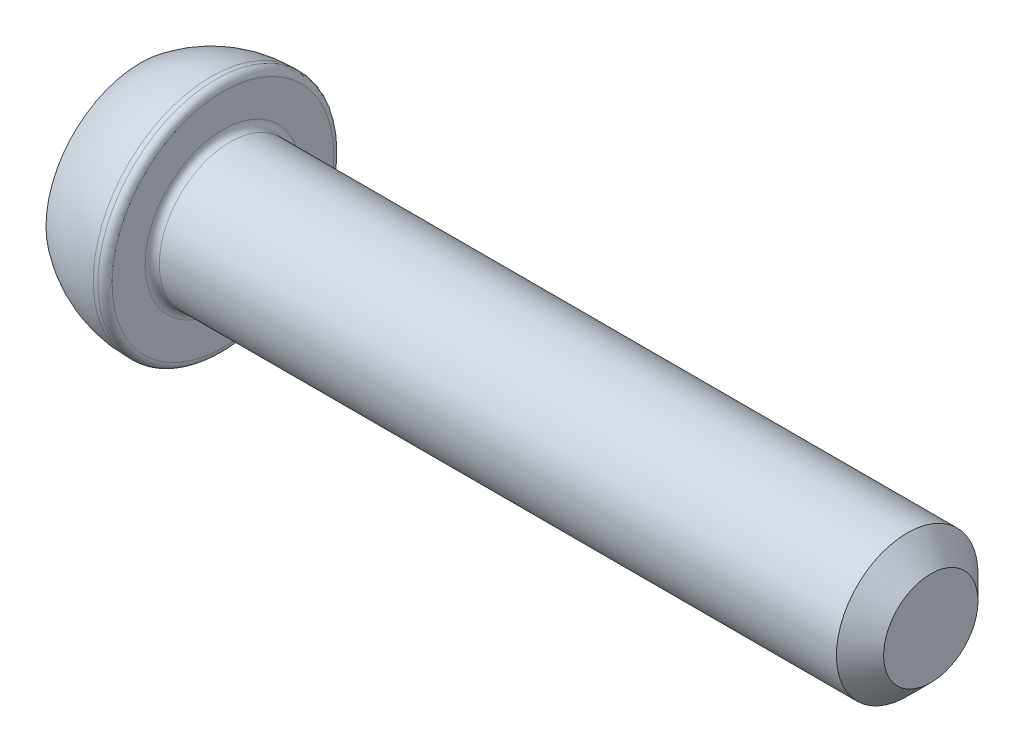
SolidWorks part; units mm, degrees
ref_plane "Спереди" through (0, 0, 0) normal (0, 0, 1) x (1, 0, 0)
ref_plane "Сверху" through (0, 0, 0) normal (0, 1, 0) x (1, 0, 0)
ref_plane "Справа" through (0, 0, 0) normal (1, 0, 0) x (0, 0, -1)
sketch "Эскиз1" plane through (0, 0, 0) normal (0, 0, 1) x (1, 0, 0)
  line L0 (0, 0) -> (0, 4)
  line L1 (3, 5) -> (3.5, 5)
  line L2 (3.5, 5) -> (3.5, 3)
  line L3 (3.5, 3) -> (33.5, 3)
  line L4 (33.5, 3) -> (33.5, 0)
  line L5 (33.5, 0) -> (0, 0) construction
  line L6 (0, 0) -> (33.5, 0)
  arc A0 (0, 4) -> (3, 5) centre (3, 0) cw
  point P9 (3.5, 4)
  dimension "D1" = 0.5
  dimension "D2" = 6
  dimension "D3" = 10
  dimension "D5" = 3.5
  dimension "D6" = 30
revolve "Повернуть1" add sketch "Эскиз1" angle 360 about L5
cosmetic thread "Условное изображение резьбы1" parameters "D2"=4.891
sketch "Эскиз2" plane through (0, 0, 0) normal (-1, 0, 0) x (0, 0, 1)
  line L1 (1.1547, 2) -> (-1.1547, 2)
  line L2 (-1.1547, 2) -> (-2.3094, 0)
  line L3 (-2.3094, 0) -> (-1.1547, -2)
  line L4 (-1.1547, -2) -> (1.1547, -2)
  line L5 (1.1547, -2) -> (2.3094, 0)
  line L6 (2.3094, 0) -> (1.1547, 2)
  circle A0 centre (0, 0) radius 2 construction
  dimension "D1" = 4
extrude "Вырез-Вытянуть1" cut sketch "Эскиз2" against normal blind 2
fillet "Скругление1" radius 0.3 2 edges at (3.5, 3, 0) (3.5, 5, 0)
chamfer "Фаска1" distance 1 angle 45 1 edges at (33.5, 3, 0)
